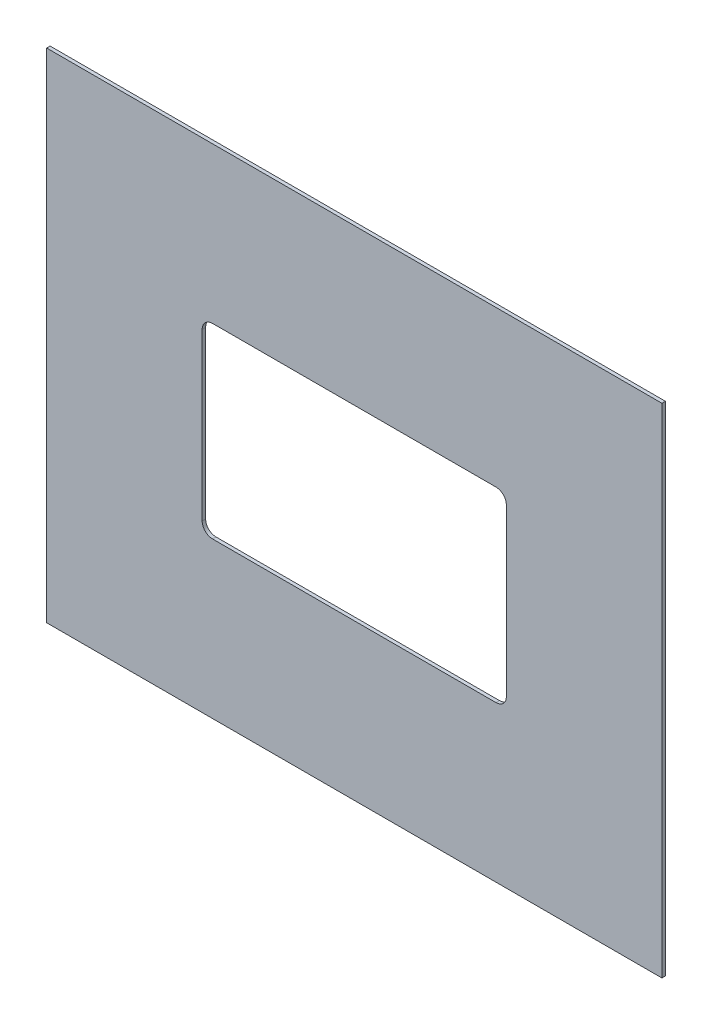
SolidWorks part; units mm, degrees
ref_plane "Front Plane" through (0, 0, 0) normal (0, 0, 1) x (1, 0, 0)
ref_plane "Top Plane" through (0, 0, 0) normal (0, 1, 0) x (1, 0, 0)
ref_plane "Right Plane" through (0, 0, 0) normal (1, 0, 0) x (0, 0, -1)
sketch "Sketch1" plane through (0, 0, 0) normal (0, 0, 1) x (1, 0, 0)
  line L0 (-86.6122, 61.3505) -> (91.3878, 61.3505)
  line L1 (-38.6122, 16.3505) -> (43.3878, 16.3505)
  line L2 (-41.6122, 13.3505) -> (-41.6122, -34.6495)
  line L3 (-38.6122, -37.6495) -> (43.3878, -37.6495)
  line L4 (46.3878, 13.3505) -> (46.3878, -34.6495)
  line L5 (91.3878, 61.3505) -> (91.3878, -82.6495)
  line L6 (-86.6122, -82.6495) -> (91.3878, -82.6495)
  line L7 (-86.6122, 61.3505) -> (-86.6122, -82.6495)
  line L8 (-41.6122, 16.3505) -> (-41.6122, -37.6495) construction
  line L9 (-41.6122, -37.6495) -> (46.3878, -37.6495) construction
  line L10 (46.3878, 16.3505) -> (46.3878, -37.6495) construction
  line L11 (-41.6122, 16.3505) -> (46.3878, 16.3505) construction
  arc A0 (-41.6122, -34.6495) -> (-38.6122, -37.6495) centre (-38.6122, -34.6495) ccw
  arc A1 (43.3878, -37.6495) -> (46.3878, -34.6495) centre (43.3878, -34.6495) ccw
  arc A2 (43.3878, 16.3505) -> (46.3878, 13.3505) centre (43.3878, 13.3505) cw
  arc A3 (-38.6122, 16.3505) -> (-41.6122, 13.3505) centre (-38.6122, 13.3505) ccw
  point P11 (-41.6122, -37.6495)
  dimension "D4" = 3
  dimension "D3" = 45
extrude "Boss-Extrude1" add sketch "Sketch1" along normal blind 1
